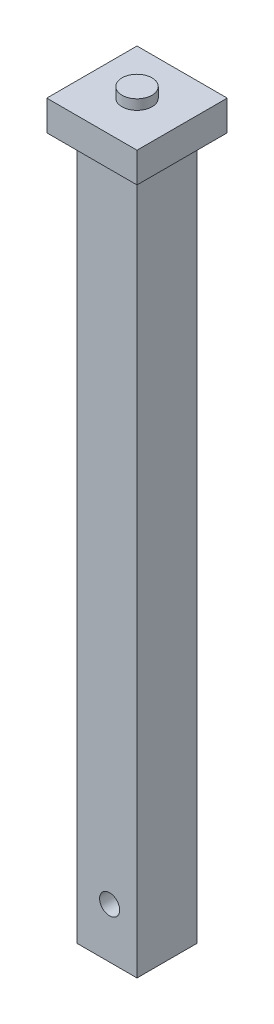
SolidWorks part; units mm, degrees
ref_plane "Front Plane" through (0, 0, 0) normal (0, 0, 1) x (1, 0, 0)
ref_plane "Top Plane" through (0, 0, 0) normal (0, 1, 0) x (1, 0, 0)
ref_plane "Right Plane" through (0, 0, 0) normal (1, 0, 0) x (0, 0, -1)
sketch "Sketch1" plane through (0, 0, 0) normal (0, 1, 0) x (1, 0, 0)
  line L1 (-45, 45) -> (45, 45)
  line L2 (-45, 45) -> (-45, -45)
  line L3 (-45, -45) -> (45, -45)
  line L4 (45, 45) -> (45, -45)
  line L5 (-45, 45) -> (45, -45) construction
  line L6 (-45, -45) -> (45, 45) construction
  point P0 (0, 0)
  dimension "D1" = 90
  dimension "D2" = 90
extrude "Boss-Extrude1" add sketch "Sketch1" along normal blind 30
sketch "Sketch2" plane through (0, 0, 0) normal (0, -1, 0) x (1, 0, 0)
  line L1 (-30, 30) -> (30, 30)
  line L2 (-30, 30) -> (-30, -30)
  line L3 (-30, -30) -> (30, -30)
  line L4 (30, 30) -> (30, -30)
  line L5 (-30, 30) -> (30, -30) construction
  line L6 (-30, -30) -> (30, 30) construction
  point P0 (0, 0)
  dimension "D1" = 60
  dimension "D2" = 60
extrude "Boss-Extrude2" add sketch "Sketch2" along normal blind 700
sketch "Sketch3" plane through (0, 0, 30) normal (0, 0, 1) x (1, 0, 0)
  line L0 (30, -700) -> (-30, -700) construction
  circle A0 centre (2.6929, -650) radius 10
  dimension "D1" = 20
  dimension "D2" = 50
extrude "Cut-Extrude1" cut sketch "Sketch3" against normal through all
sketch "Sketch4" plane through (0, 30, 0) normal (0, 1, 0) x (1, 0, 0)
  circle A0 centre (0, 0) radius 15
  dimension "D1" = 30
extrude "Boss-Extrude3" add sketch "Sketch4" along normal blind 10
